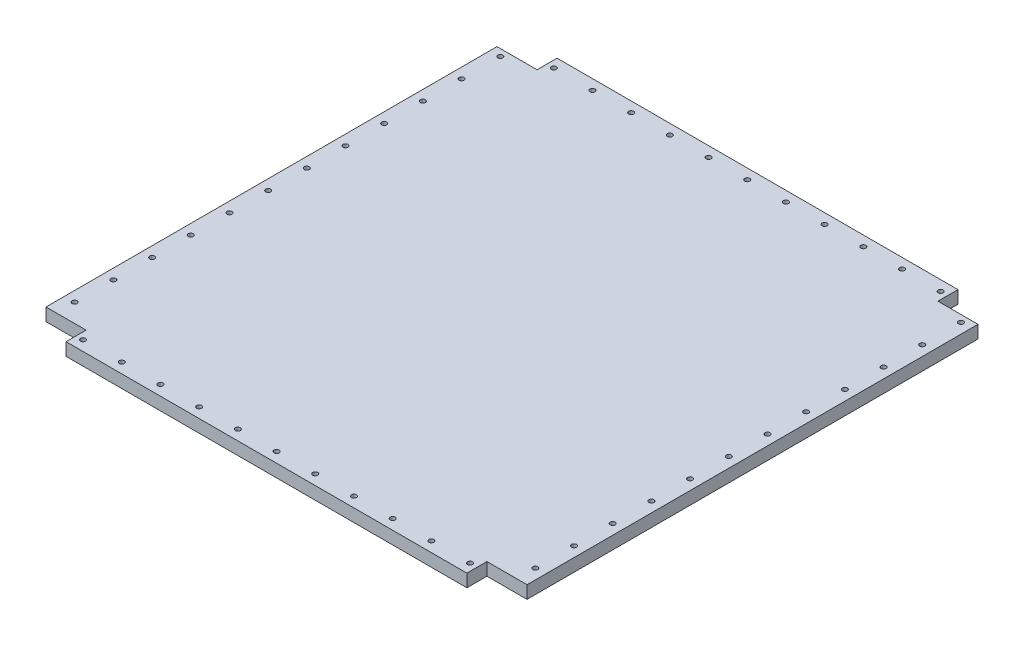
SolidWorks part; units mm, degrees
ref_plane "Front Plane" through (0, 0, 0) normal (0, 0, 1) x (1, 0, 0)
ref_plane "Top Plane" through (0, 0, 0) normal (0, 1, 0) x (1, 0, 0)
ref_plane "Right Plane" through (0, 0, 0) normal (1, 0, 0) x (0, 0, -1)
sketch "Sketch1" plane through (0, 0, 0) normal (0, 1, 0) x (1, 0, 0)
  line L0 (-199.531, 245.6001) -> (200.469, 245.6001)
  line L1 (200.469, 225.6001) -> (240.469, 225.6001)
  line L2 (240.469, 225.6001) -> (240.469, -224.3999)
  line L3 (240.469, -224.3999) -> (200.469, -224.3999)
  line L4 (200.469, -224.3999) -> (200.469, -244.3999)
  line L5 (200.469, -244.3999) -> (-199.531, -244.3999)
  line L6 (-199.531, -244.3999) -> (-199.531, -224.3999)
  line L7 (-199.531, -224.3999) -> (-239.531, -224.3999)
  line L8 (-239.531, -224.3999) -> (-239.531, 225.6001)
  line L9 (-239.531, 225.6001) -> (-199.531, 225.6001)
  line L10 (-199.531, 225.6001) -> (-199.531, 245.6001)
  line L11 (200.469, 245.6001) -> (200.469, 225.6001)
  dimension "D1" = 400
  dimension "D2" = 20
  dimension "D3" = 40
  dimension "D4" = 450
  dimension "D5" = 40
  dimension "D6" = 20
  dimension "D7" = 400
  dimension "D8" = 20
  dimension "D9" = 40
  dimension "D10" = 450
extrude "Boss-Extrude1" add sketch "Sketch1" along normal blind 12.7
sketch "Sketch2" plane through (0, 12.7, 0) normal (0, 1, 0) x (1, 0, 0)
  line L0 (200.469, 245.6001) -> (-199.531, 245.6001) construction
  line L1 (-199.531, 245.6001) -> (-199.531, 225.6001) construction
  circle A0 centre (-192.673, 235.4401) radius 2.5
  dimension "D1" = 5
  dimension "D2" = 10.16
  dimension "D3" = 6.858
extrude "Cut-Extrude1" cut sketch "Sketch2" against normal through all both and the other way through all
pattern_linear "LPattern1" count 11 spacing 38.608 along (1, 0, 0) of "Cut-Extrude1"
sketch "Sketch3" plane through (0, 12.7, 0) normal (0, 1, 0) x (1, 0, 0)
  line L0 (-199.531, -244.3999) -> (200.469, -244.3999) construction
  line L1 (-199.531, -224.3999) -> (-199.531, -244.3999) construction
  circle A0 centre (-192.673, -234.2399) radius 2.5
  dimension "D1" = 5
  dimension "D2" = 10.16
  dimension "D3" = 6.858
extrude "Cut-Extrude2" cut sketch "Sketch3" against normal through all both
pattern_linear "LPattern2" count 11 spacing 38.608 along (1, 0, 0) of "Cut-Extrude2"
sketch "Sketch4" plane through (0, 12.7, 0) normal (0, 1, 0) x (1, 0, 0)
  line L0 (240.469, -224.3999) -> (240.469, 225.6001) construction
  line L1 (240.469, 225.6001) -> (200.469, 225.6001) construction
  circle A0 centre (230.309, 218.7421) radius 2.5
  dimension "D1" = 5
  dimension "D2" = 10.16
  dimension "D3" = 6.858
extrude "Cut-Extrude3" cut sketch "Sketch4" against normal through all both
pattern_linear "LPattern3" count 12 spacing 38.608 along (0, 0, 1) of "Cut-Extrude3"
sketch "Sketch5" plane through (0, 12.7, 0) normal (0, 1, 0) x (1, 0, 0)
  line L0 (-199.531, 225.6001) -> (-239.531, 225.6001) construction
  line L1 (-239.531, 225.6001) -> (-239.531, -224.3999) construction
  circle A0 centre (-229.371, 218.7421) radius 2.5
  dimension "D1" = 6.858
  dimension "D2" = 5
  dimension "D3" = 10.16
extrude "Cut-Extrude4" cut sketch "Sketch5" against normal through all both
pattern_linear "LPattern4" count 12 spacing 38.608 along (0, 0, 1) of "Cut-Extrude4"
